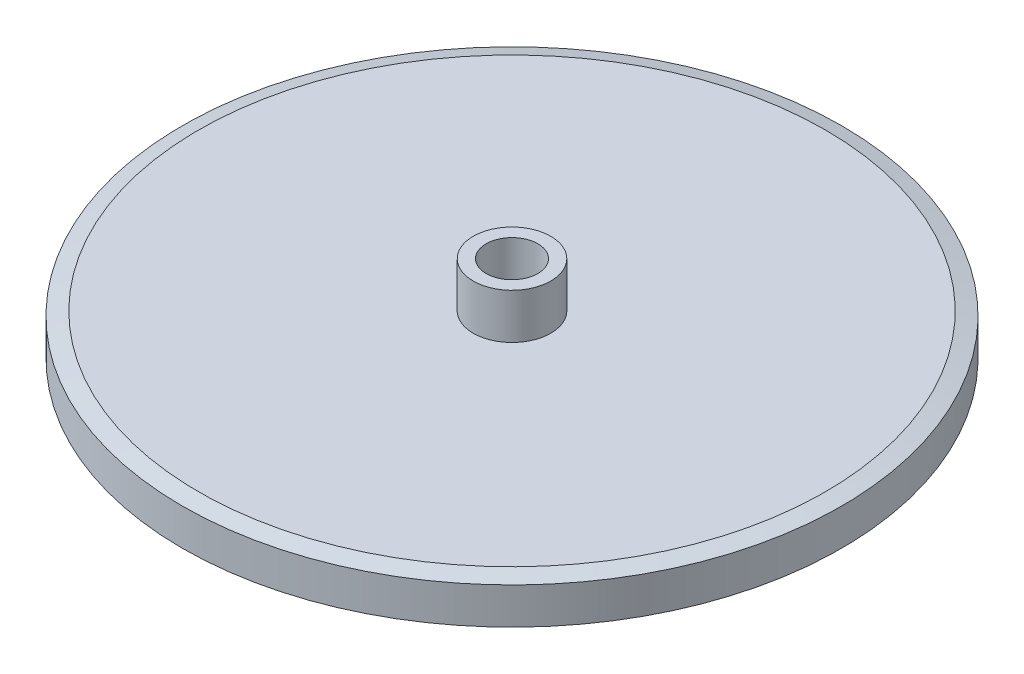
SolidWorks part; units mm, degrees
material "Сталь ШХ15 ГОСТ 801-78"
ref_plane "Plane1" through (0, 0, 0) normal (0, 0, 1) x (1, 0, 0)
ref_plane "Plane2" through (0, 0, 0) normal (0, 1, 0) x (1, 0, 0)
ref_plane "Plane3" through (0, 0, 0) normal (1, 0, 0) x (0, 0, -1)
sketch "Эскиз1" plane through (0, 0, 0) normal (0, 0, 1) x (1, 0, 0)
  line L0 (0, 0) -> (25.5, 0)
  line L1 (25.5, 0) -> (25.5, 3.5)
  line L2 (25.5, 3.5) -> (3, 3.5)
  line L3 (3, 3.5) -> (3, 7)
  line L4 (3, 7) -> (0, 7)
  line L5 (0, 7) -> (0, 0)
  dimension "D1" = 3.5
  dimension "30" = 25.5
  dimension "D3" = 3
  dimension "D4" = 3.5
ref_axis "Ось1" through (0, 7, 0) along (0, -1, 0)
revolve "Повернуть2" add sketch "Эскиз1" angle 360 about axis through (0, 7, 0) along (0, -1, 0)
chamfer "Фаска1" distance 1.25 angle 15 1 edges at (0, 3.5, 25.5)
sketch "Эскиз2" plane through (0, 0, 0) normal (0, -1, 0) x (-1, 0, 0)
  circle A0 centre (0, 0) radius 2
  dimension "D1" = 4
sketch "Эскиз3" plane through (0, 0, 0) normal (1, 0, 0) x (0, 0, -1)
  circle A0 centre (0, 7.4791) radius 1
extrude "Вырез-Вытянуть3" cut sketch "Эскиз2" against normal through all both
chamfer "Фаска2" distance 1.25 angle 15 1 edges at (0, 0, 25.5)
